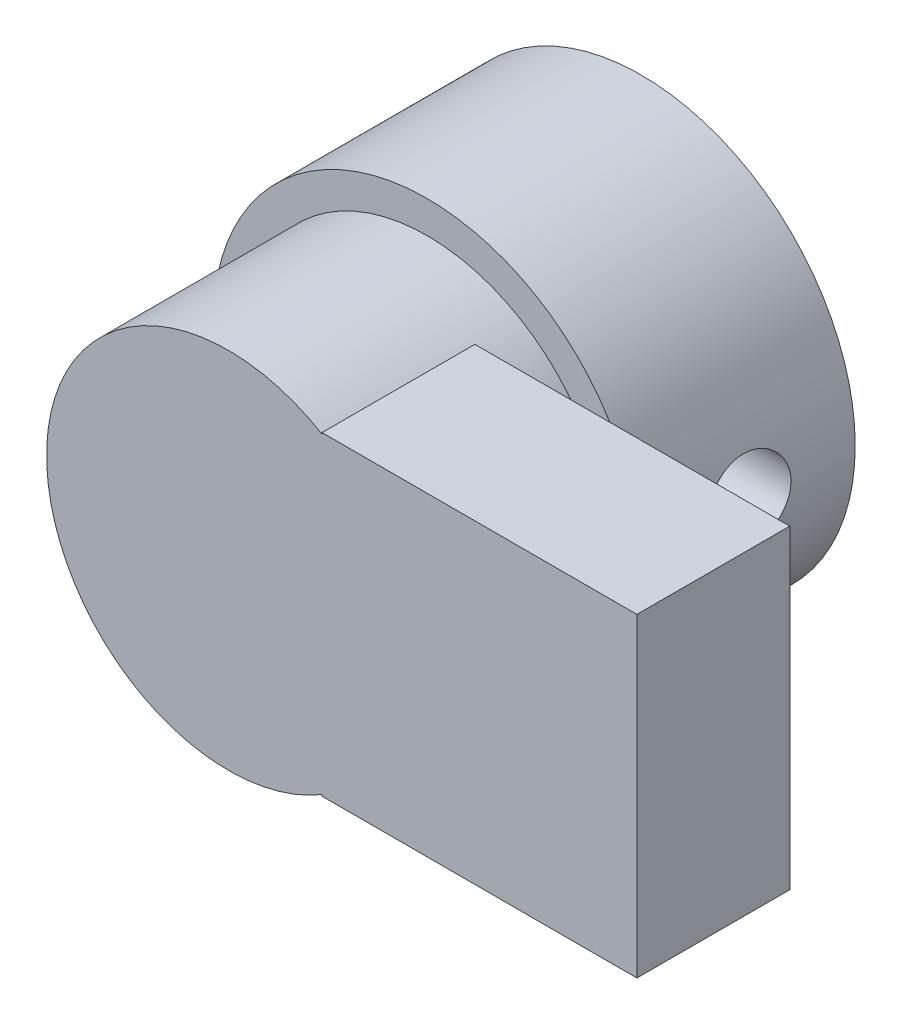
SolidWorks part; units mm, degrees
ref_plane "Front Plane" through (0, 0, 0) normal (0, 0, 1) x (1, 0, 0)
ref_plane "Top Plane" through (0, 0, 0) normal (0, 1, 0) x (1, 0, 0)
ref_plane "Right Plane" through (0, 0, 0) normal (1, 0, 0) x (0, 0, -1)
sketch "Sketch1" plane through (0, 0, 0) normal (0, 0, 1) x (1, 0, 0)
  circle A0 centre (-3.8923, 1.8206) radius 7
  circle A1 centre (-3.8923, 1.8206) radius 4.075
  dimension "D1" = 14
  dimension "D2" = 0
  dimension "D3" = 8.15
extrude "Boss-Extrude1" add sketch "Sketch1" along normal blind 7
sketch "Sketch2" plane through (0, 0, 7) normal (0, 0, 1) x (1, 0, 0)
  circle A0 centre (-3.8923, 1.8206) radius 5.95
  circle A1 centre (-3.8923, 1.8206) radius 7 construction
  dimension "11.85" = 11.9
  dimension "D1" = 0
extrude "Boss-Extrude2" add sketch "Sketch2" along normal blind 1.5
sketch "Sketch3" plane through (0, 0, 8.5) normal (0, 0, 1) x (1, 0, 0)
  line L1 (9.4668, 6.9706) -> (-0.8332, 6.9706)
  line L2 (9.4668, 6.9706) -> (9.4668, -3.3294)
  line L3 (9.4668, -3.3294) -> (-0.8332, -3.3294)
  line L4 (-0.8332, 6.9706) -> (-0.8332, -3.3294)
  circle A0 centre (-3.8923, 1.8206) radius 5.95 construction
  circle A1 centre (-3.8923, 1.8206) radius 5.95
  circle M1 centre (-3.8923, 1.8206) radius 5.95
  dimension "D5" = 0
  dimension "D6" = 11.9
  dimension "D1" = 5.99
  dimension "D2" = 5.99
  dimension "D3" = 10.3
  dimension "D4" = 10.3
extrude "Boss-Extrude3" add sketch "Sketch3" along normal blind 5 contours L3 L2 L1 M1 | L4 M1 | L4 M1
sketch "Sketch4" plane through (9.4668, 0, 0) normal (1, 0, 0) x (0, 0, -1)
  line L0 (-7, 8.8206) -> (-7, -5.1794) construction
  line L1 (-13.5, 6.9706) -> (-8.5, 6.9706) construction
  circle A0 centre (-3.5, 1.8706) radius 1.4
  dimension "D1" = 2.8
  dimension "D2" = 3.5
  dimension "D3" = 5.1
extrude "Cut-Extrude2" cut sketch "Sketch4" against normal blind 10
